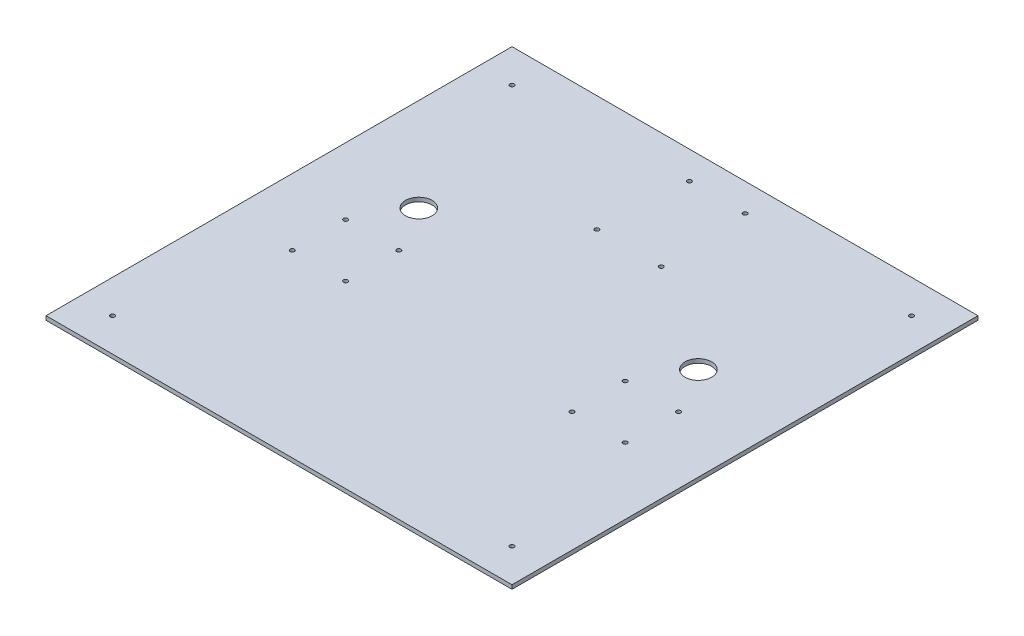
SolidWorks part; units mm, degrees
ref_plane "Front Plane" through (0, 0, 0) normal (0, 0, 1) x (1, 0, 0)
ref_plane "Top Plane" through (0, 0, 0) normal (0, 1, 0) x (1, 0, 0)
ref_plane "Right Plane" through (0, 0, 0) normal (1, 0, 0) x (0, 0, -1)
sketch "Sketch1" plane through (0, 0, 0) normal (0, 1, 0) x (1, 0, 0)
  line L1 (-175, -175) -> (175, -175)
  line L2 (-175, -175) -> (-175, 175)
  line L3 (-175, 175) -> (175, 175)
  line L4 (175, -175) -> (175, 175)
  line L5 (-175, -175) -> (175, 175) construction
  line L6 (-175, 175) -> (175, -175) construction
  circle A0 centre (-150, 150) radius 1.6
  circle A1 centre (-150, -150) radius 1.6
  circle A3 centre (150, -150) radius 1.6
  circle A5 centre (150, 150) radius 1.6
  point P0 (0, 0)
  dimension "D1" = 350
  dimension "D2" = 350
extrude "Boss-Extrude1" add sketch "Sketch1" along normal blind 3
sketch "Sketch2" plane through (0, 3, 0) normal (0, 1, 0) x (1, 0, 0)
  line L0 (0.0934, 154.0285) -> (0.0934, 87.9285) construction
  line L1 (-24.2344, 87.9285) -> (24.1556, 87.9285) construction
  line L3 (21.0484, 154.0285) -> (-20.8616, 154.0285) construction
  line L4 (-125, 0) -> (-85, 0) construction
  line L5 (-85, 0) -> (-85, -40) construction
  line L6 (85, 0) -> (125, 0) construction
  line L7 (125, 0) -> (125, -40) construction
  circle A0 centre (-105, 35) radius 10
  circle A1 centre (105, 35) radius 10
  circle A2 centre (-20.8616, 154.0285) radius 1.6
  circle A3 centre (-24.2344, 87.9285) radius 1.6
  circle A4 centre (21.0484, 154.0285) radius 1.6
  circle A5 centre (24.1556, 87.9285) radius 1.6
  circle A10 centre (-125, 0) radius 1.6
  circle A11 centre (-85, 0) radius 1.6
  circle A12 centre (-125, -40) radius 1.6
  circle A13 centre (-85, -40) radius 1.6
  circle A14 centre (85, 0) radius 1.6
  circle A15 centre (125, 0) radius 1.6
  circle A16 centre (85, -40) radius 1.6
  circle A17 centre (125, -40) radius 1.6
extrude "Cut-Extrude1" cut sketch "Sketch2" against normal blind 3
